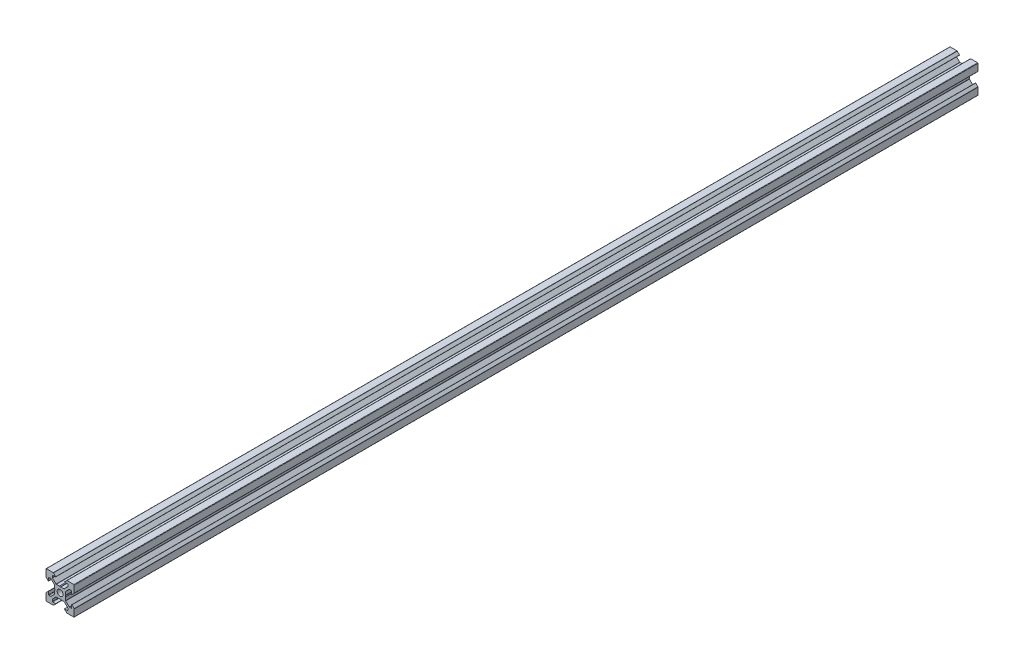
SolidWorks part; units mm, degrees
material "6063-T5"
ref_plane "Plan de face" through (0, 0, 0) normal (0, 0, 1) x (1, 0, 0)
ref_plane "Plan de dessus" through (0, 0, 0) normal (0, 1, 0) x (1, 0, 0)
ref_plane "Plan de droite" through (0, 0, 0) normal (1, 0, 0) x (0, 0, -1)
sketch "Esquisse1" plane through (0, 0, 0) normal (0, 0, 1) x (1, 0, 0)
  line L0 (18.7749, -2.8952) -> (18.7749, -4.8946)
  line L1 (18.4749, -5.1946) -> (17.2591, -5.1946)
  line L2 (17.047, -5.1067) -> (14.5634, -2.6231)
  line L3 (14.4755, -2.411) -> (14.4755, -0.2148)
  line L4 (14.4755, -0.2148) -> (14.1755, 0.3048)
  line L5 (14.1755, 0.3048) -> (14.4755, 0.8244)
  line L6 (14.4755, 0.8244) -> (14.4755, 3.0205)
  line L7 (14.5634, 3.2326) -> (17.047, 5.7162)
  line L8 (17.2591, 5.8041) -> (18.4749, 5.8041)
  line L9 (18.7749, 5.5041) -> (18.7749, 3.5048)
  line L10 (18.9456, 3.4341) -> (20.487, 4.9755)
  line L11 (20.5749, 5.1876) -> (20.5749, 10.0048)
  line L12 (20.2749, 10.3048) -> (15.4577, 10.3048)
  line L13 (15.2456, 10.2169) -> (13.7041, 8.6755)
  line L14 (13.7749, 8.5048) -> (15.7742, 8.5048)
  line L15 (16.0742, 8.2048) -> (16.0742, 6.989)
  line L16 (15.9863, 6.7769) -> (13.5027, 4.2933)
  line L17 (13.2906, 4.2054) -> (11.0945, 4.2054)
  line L18 (11.0945, 4.2054) -> (10.5749, 3.9054)
  line L19 (10.5749, 3.9054) -> (10.0552, 4.2054)
  line L20 (10.0552, 4.2054) -> (7.8591, 4.2054)
  line L21 (7.647, 4.2933) -> (5.1634, 6.7769)
  line L22 (5.0755, 6.989) -> (5.0755, 8.2048)
  line L23 (5.3755, 8.5048) -> (7.3749, 8.5048)
  line L24 (7.4456, 8.6755) -> (5.9041, 10.2169)
  line L25 (5.692, 10.3048) -> (0.8749, 10.3048)
  line L26 (0.5749, 10.0048) -> (0.5749, 5.1876)
  line L27 (0.6627, 4.9755) -> (2.2041, 3.4341)
  line L28 (2.3749, 3.5048) -> (2.3749, 5.5041)
  line L29 (2.6749, 5.8041) -> (3.8906, 5.8041)
  line L30 (4.1027, 5.7162) -> (6.5863, 3.2326)
  line L31 (6.6742, 3.0205) -> (6.6742, 0.8244)
  line L32 (6.6742, 0.8244) -> (6.9742, 0.3048)
  line L33 (6.9742, 0.3048) -> (6.6742, -0.2148)
  line L34 (6.6742, -0.2148) -> (6.6742, -2.411)
  line L35 (6.5863, -2.6231) -> (4.1027, -5.1067)
  line L36 (3.8906, -5.1946) -> (2.6749, -5.1946)
  line L37 (2.3749, -4.8946) -> (2.3749, -2.8952)
  line L38 (2.2041, -2.8245) -> (0.6627, -4.3659)
  line L39 (0.5749, -4.5781) -> (0.5749, -9.3952)
  line L40 (0.8749, -9.6952) -> (5.692, -9.6952)
  line L41 (5.9041, -9.6074) -> (7.4456, -8.0659)
  line L42 (7.3749, -7.8952) -> (5.3755, -7.8952)
  line L43 (5.0755, -7.5952) -> (5.0755, -6.3795)
  line L44 (5.1634, -6.1674) -> (7.647, -3.6838)
  line L45 (7.8591, -3.5959) -> (10.0552, -3.5959)
  line L46 (10.0552, -3.5959) -> (10.5749, -3.2959)
  line L47 (10.5749, -3.2959) -> (11.0945, -3.5959)
  line L48 (11.0945, -3.5959) -> (13.2906, -3.5959)
  line L49 (13.5027, -3.6838) -> (15.9863, -6.1674)
  line L50 (16.0742, -6.3795) -> (16.0742, -7.5952)
  line L51 (15.7742, -7.8952) -> (13.7749, -7.8952)
  line L52 (13.7041, -8.0659) -> (15.2456, -9.6074)
  line L53 (15.4577, -9.6952) -> (20.2749, -9.6952)
  line L54 (20.5749, -9.3952) -> (20.5749, -4.5781)
  line L55 (20.487, -4.3659) -> (18.9456, -2.8245)
  arc A0 (10.5749, -1.7952) -> (12.6749, 0.3048) centre (10.5749, 0.3048) ccw
  arc A1 (12.6749, 0.3048) -> (10.5749, 2.4048) centre (10.5749, 0.3048) ccw
  arc A2 (10.5749, 2.4048) -> (8.4749, 0.3048) centre (10.5749, 0.3048) ccw
  arc A3 (8.4749, 0.3048) -> (10.5749, -1.7952) centre (10.5749, 0.3048) ccw
  arc A4 (18.9456, -2.8245) -> (18.7749, -2.8952) centre (18.8749, -2.8952) ccw
  arc A5 (18.4749, -5.1946) -> (18.7749, -4.8946) centre (18.4749, -4.8946) ccw
  arc A6 (17.047, -5.1067) -> (17.2591, -5.1946) centre (17.2591, -4.8946) ccw
  arc A7 (14.4755, -2.411) -> (14.5634, -2.6231) centre (14.7755, -2.411) ccw
  arc A8 (14.5634, 3.2326) -> (14.4755, 3.0205) centre (14.7755, 3.0205) ccw
  arc A9 (17.2591, 5.8041) -> (17.047, 5.7162) centre (17.2591, 5.5041) ccw
  arc A10 (18.7749, 5.5041) -> (18.4749, 5.8041) centre (18.4749, 5.5041) ccw
  arc A11 (18.7749, 3.5048) -> (18.9456, 3.4341) centre (18.8749, 3.5048) ccw
  arc A12 (20.487, 4.9755) -> (20.5749, 5.1876) centre (20.2749, 5.1876) ccw
  arc A13 (20.5749, 10.0048) -> (20.2749, 10.3048) centre (20.2749, 10.0048) ccw
  arc A14 (15.4577, 10.3048) -> (15.2456, 10.2169) centre (15.4577, 10.0048) ccw
  arc A15 (13.7041, 8.6755) -> (13.7749, 8.5048) centre (13.7749, 8.6048) ccw
  arc A16 (16.0742, 8.2048) -> (15.7742, 8.5048) centre (15.7742, 8.2048) ccw
  arc A17 (15.9863, 6.7769) -> (16.0742, 6.989) centre (15.7742, 6.989) ccw
  arc A18 (13.2906, 4.2054) -> (13.5027, 4.2933) centre (13.2906, 4.5054) ccw
  arc A19 (7.647, 4.2933) -> (7.8591, 4.2054) centre (7.8591, 4.5054) ccw
  arc A20 (5.0755, 6.989) -> (5.1634, 6.7769) centre (5.3755, 6.989) ccw
  arc A21 (5.3755, 8.5048) -> (5.0755, 8.2048) centre (5.3755, 8.2048) ccw
  arc A22 (7.3749, 8.5048) -> (7.4456, 8.6755) centre (7.3749, 8.6048) ccw
  arc A23 (5.9041, 10.2169) -> (5.692, 10.3048) centre (5.692, 10.0048) ccw
  arc A24 (0.8749, 10.3048) -> (0.5749, 10.0048) centre (0.8749, 10.0048) ccw
  arc A25 (0.5749, 5.1876) -> (0.6627, 4.9755) centre (0.8749, 5.1876) ccw
  arc A26 (2.2041, 3.4341) -> (2.3749, 3.5048) centre (2.2749, 3.5048) ccw
  arc A27 (2.6749, 5.8041) -> (2.3749, 5.5041) centre (2.6749, 5.5041) ccw
  arc A28 (4.1027, 5.7162) -> (3.8906, 5.8041) centre (3.8906, 5.5041) ccw
  arc A29 (6.6742, 3.0205) -> (6.5863, 3.2326) centre (6.3742, 3.0205) ccw
  arc A30 (6.5863, -2.6231) -> (6.6742, -2.411) centre (6.3742, -2.411) ccw
  arc A31 (3.8906, -5.1946) -> (4.1027, -5.1067) centre (3.8906, -4.8946) ccw
  arc A32 (2.3749, -4.8946) -> (2.6749, -5.1946) centre (2.6749, -4.8946) ccw
  arc A33 (2.3749, -2.8952) -> (2.2041, -2.8245) centre (2.2749, -2.8952) ccw
  arc A34 (0.6627, -4.3659) -> (0.5749, -4.5781) centre (0.8749, -4.5781) ccw
  arc A35 (0.5749, -9.3952) -> (0.8749, -9.6952) centre (0.8749, -9.3952) ccw
  arc A36 (5.692, -9.6952) -> (5.9041, -9.6074) centre (5.692, -9.3952) ccw
  arc A37 (7.4456, -8.0659) -> (7.3749, -7.8952) centre (7.3749, -7.9952) ccw
  arc A38 (5.0755, -7.5952) -> (5.3755, -7.8952) centre (5.3755, -7.5952) ccw
  arc A39 (5.1634, -6.1674) -> (5.0755, -6.3795) centre (5.3755, -6.3795) ccw
  arc A40 (7.8591, -3.5959) -> (7.647, -3.6838) centre (7.8591, -3.8959) ccw
  arc A41 (13.5027, -3.6838) -> (13.2906, -3.5959) centre (13.2906, -3.8959) ccw
  arc A42 (16.0742, -6.3795) -> (15.9863, -6.1674) centre (15.7742, -6.3795) ccw
  arc A43 (15.7742, -7.8952) -> (16.0742, -7.5952) centre (15.7742, -7.5952) ccw
  arc A44 (13.7749, -7.8952) -> (13.7041, -8.0659) centre (13.7749, -7.9952) ccw
  arc A45 (15.2456, -9.6074) -> (15.4577, -9.6952) centre (15.4577, -9.3952) ccw
  arc A46 (20.2749, -9.6952) -> (20.5749, -9.3952) centre (20.2749, -9.3952) ccw
  arc A47 (20.5749, -4.5781) -> (20.487, -4.3659) centre (20.2749, -4.5781) ccw
extrude "Boss.-Extru.1" add sketch "Esquisse1" along normal blind 640
